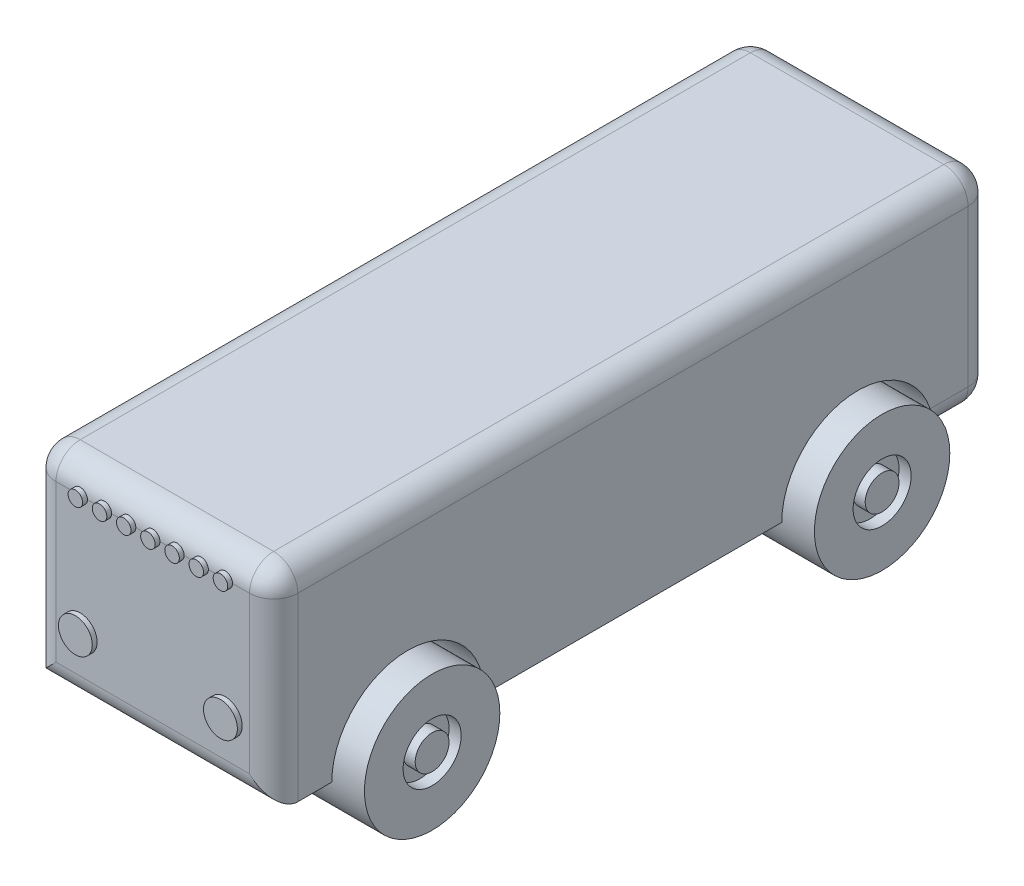
SolidWorks part; units mm, degrees
ref_plane "Спереди" through (0, 0, 0) normal (0, 0, 1) x (1, 0, 0)
ref_plane "Сверху" through (0, 0, 0) normal (0, 1, 0) x (1, 0, 0)
ref_plane "Справа" through (0, 0, 0) normal (1, 0, 0) x (0, 0, -1)
sketch "Эскиз1" plane through (0, 0, 0) normal (1, 0, 0) x (0, 0, -1)
  line L0 (-148.5757, -17.3338) -> (-124.5379, -17.3338)
  line L2 (-148.5757, 17.3338) -> (-148.5757, -17.3338)
  line L3 (-148.5757, -17.3338) -> (-124.5379, -17.3338)
  line L4 (148.5757, 17.3338) -> (148.5757, -17.3338)
  line L9 (124.5379, -17.3338) -> (148.5757, -17.3338)
  line L11 (-148.5757, 17.3338) -> (-148.5757, 32.3338)
  line L12 (-148.5757, 32.3338) -> (148.5757, 32.3338)
  line L13 (148.5757, 17.3338) -> (148.5757, 32.3338)
  line L15 (-61.5379, -17.3338) -> (61.5379, -17.3338)
  arc A0 (-61.5379, -17.3338) -> (-124.5379, -17.3338) centre (-93.0379, -17.3338) ccw
  arc A1 (61.5379, -17.3338) -> (124.5379, -17.3338) centre (93.0379, -17.3338) cw
  point P0 (0, 0)
  dimension "D3" = 15
extrude "Бобышка-Вытянуть1" add sketch "Эскиз1" along normal blind 100 contours L15 A1 L9 L4 L13 L12 L11 L2 L0 A0
sketch "Эскиз2" plane through (0, 0, 0) normal (1, 0, 0) x (0, 0, -1)
  line L0 (-124.5379, -17.3338) -> (-61.5379, -17.3338) construction
  line L1 (61.5379, -17.3338) -> (124.5379, -17.3338) construction
  circle A0 centre (-93.0379, -17.3338) radius 28
  circle A1 centre (93.0379, -17.3338) radius 28
extrude "Бобышка-Вытянуть2" add sketch "Эскиз2" along normal blind 30 and the other way blind 10 separate body
sketch "Эскиз3" plane through (100, 0, 0) normal (1, 0, 0) x (0, 0, -1)
  line L0 (-124.5379, -17.3338) -> (-61.5379, -17.3338) construction
  line L1 (61.5379, -17.3338) -> (124.5379, -17.3338) construction
  arc A0 (-61.5379, -17.3338) -> (-124.5379, -17.3338) centre (-93.0379, -17.3338) ccw construction
  circle A1 centre (-93.0379, -17.3338) radius 28
  circle A2 centre (93.0379, -17.3338) radius 28
extrude "Бобышка-Вытянуть3" add sketch "Эскиз3" against normal blind 30 and the other way blind 10 separate body
sketch "Эскиз4" plane through (0, -17.3338, 0) normal (0, -1, 0) x (1, 0, 0)
  line L0 (0, 61.5379) -> (50, 61.5379) construction
  line L1 (100, 61.5379) -> (0, 61.5379) construction
  line L3 (100, 124.5379) -> (0, 124.5379) construction
  line L4 (0, 0) -> (150.4034, 0) construction
  line L5 (45, 61.5379) -> (55, 61.5379)
  line L6 (45, 61.5379) -> (45, 88.0379)
  line L7 (45, 124.5379) -> (55, 124.5379)
  line L8 (55, 61.5379) -> (55, 88.0379)
  line L11 (70.0613, 88.0379) -> (55, 88.0379)
  line L12 (70.0613, 88.0379) -> (70.0613, 98.0379)
  line L13 (70.0613, 98.0379) -> (55, 98.0379)
  line L14 (29.9387, 88.0379) -> (29.9387, 98.0379)
  line L17 (150.4034, 0) -> (-75.8776, 0) construction
  line L18 (45, -61.5379) -> (55, -61.5379)
  line L19 (45, -124.5379) -> (55, -124.5379)
  line L20 (29.9387, -88.0379) -> (29.9387, -98.0379)
  line L21 (70.0613, -88.0379) -> (70.0613, -98.0379)
  line L22 (70.0613, -88.0379) -> (55, -88.0379)
  line L23 (70.0613, -98.0379) -> (55, -98.0379)
  line L24 (55, -61.5379) -> (55, -88.0379)
  line L25 (45, -61.5379) -> (45, -88.0379)
  line L26 (45, -98.0379) -> (45, -124.5379)
  line L27 (45, -98.0379) -> (29.9387, -98.0379)
  line L28 (45, -88.0379) -> (29.9387, -88.0379)
  line L29 (55, -98.0379) -> (55, -124.5379)
  line L30 (45, 88.0379) -> (29.9387, 88.0379)
  line L32 (45, 98.0379) -> (45, 124.5379)
  line L33 (45, 98.0379) -> (29.9387, 98.0379)
  line L34 (55, 98.0379) -> (55, 124.5379)
  point P5 (50, 93.0379)
  point P13 (50, 93.0379)
  dimension "D1" = 10
  dimension "D2" = 10
extrude "Бобышка-Вытянуть5" add sketch "Эскиз4" against normal blind 10 contours L5 L8 L11 L12 L13 L34 L7 L32 L33 L14 L30 L6 | L18 L24 L22 L21 L23 L29 L19 L26 L27 L20 L28 L25
sketch "Эскиз7" plane through (0, 0, 0) normal (1, 0, 0) x (0, 0, -1)
  line L1 (-148.5757, 32.3338) -> (148.5757, 32.3338)
  line L2 (-148.5757, 32.3338) -> (-148.5757, 57.3338)
  line L3 (-138.5757, 67.3338) -> (138.5757, 67.3338)
  line L4 (148.5757, 32.3338) -> (148.5757, 57.3338)
  arc A0 (-148.5757, 57.3338) -> (-138.5757, 67.3338) centre (-138.5757, 57.3338) cw
  arc A1 (148.5757, 57.3338) -> (138.5757, 67.3338) centre (138.5757, 57.3338) ccw
  point P7 (-148.5757, 67.3338)
  dimension "D2" = 10
  dimension "D3" = 10
  dimension "D1" = 35
extrude "Бобышка-Вытянуть7" add sketch "Эскиз7" along normal blind 100
sketch "Эскиз9" plane through (0, 0, 0) normal (0, 0, 1) x (1, 0, 0)
  line L0 (0, -7.3248) -> (50, -7.3248)
  line L1 (0, -17.3338) -> (0, 57.3338) construction
  line L2 (50, -7.3248) -> (100, -7.3248)
  line L3 (100, -17.3338) -> (100, 57.3338) construction
  line L4 (100, -7.3248) -> (75, -7.3248)
  line L5 (25, -7.3248) -> (50, -7.3248)
  line L6 (25, -7.3248) -> (12.5, -7.3248)
  line L7 (75, -7.3248) -> (87.5, -7.3248)
  dimension "D1" = 50
  dimension "D2" = 12.5
  dimension "D3" = 12.5
fillet "Скругление1" radius 10 11 edges at (100, 20, -148.5757) (0, 64.4049, -145.6468) (100, 64.4049, -145.6468) (0, 67.3338, 0) (100, 67.3338, 0) (0, 64.4049, 145.6468) (100, 64.4049, 145.6468) (0, 20, -148.5757) (100, 20, 148.5757) (50, -17.3338, 148.5757) (0, 20, 148.5757)
fillet "Скругление2" radius 10 5 edges at (100, -17.3338, -131.5568) (97.0711, -17.3338, -145.6468) (0, -17.3338, -131.5568) (2.9289, -17.3338, -145.6468) (50, -17.3338, -148.5757)
sketch "Эскиз10" plane through (0, 0, 148.5757) normal (0, 0, 1) x (1, 0, 0)
  line L0 (10, -1.617) -> (50, -1.617)
  line L1 (10, 57.3338) -> (10, -7.3338) construction
  line L2 (50, -1.617) -> (90, -1.617)
  line L3 (90, -7.3338) -> (90, 57.3338) construction
  line L4 (90, -1.617) -> (70, -1.617)
  line L5 (70, -1.617) -> (30, -1.617)
  line L6 (30, -1.617) -> (20, -1.617)
  line L7 (50, 48.2611) -> (50, -1.617)
  line L8 (90, 57.3338) -> (10, 57.3338) construction
  line L9 (15, 60.3338) -> (85, 60.3338)
  line L10 (15, 60.3338) -> (15, 54.3338)
  line L11 (15, 54.3338) -> (85, 54.3338)
  line L12 (85, 60.3338) -> (85, 54.3338)
  circle A0 centre (20, 8.3202) radius 7
  circle A1 centre (80, 8.3202) radius 7
  circle A2 centre (50, 57.3338) radius 3
  circle A3 centre (60, 57.3338) radius 3
  circle A4 centre (70, 57.3338) radius 3
  circle A5 centre (80, 57.3338) radius 3
  circle A6 centre (40, 57.3338) radius 3
  circle A7 centre (30, 57.3338) radius 3
  circle A8 centre (20, 57.3338) radius 3
  point P15 (50, 57.3338)
  line M14 (90, 57.3338) -> (10, 57.3338)
  dimension "D3" = 70
  dimension "D1" = 40
  dimension "D2" = 10
  dimension "D4" = 6
  dimension "D5" = 4
  dimension "D6" = 4
extrude "Бобышка-Вытянуть9" add sketch "Эскиз10" along normal blind 2 contours A0 | A1 | A8 M14 | A8 M14 | A7 M14 | A7 M14 | A6 M14 | A6 M14 | A2 M14 | A2 M14 | A3 M14 | A3 M14 | A4 M14 | A4 M14 | A5 M14 | A5 M14
sketch "Эскиз11" plane through (-10, 0, 0) normal (-1, 0, 0) x (0, 0, 1)
  circle A0 centre (-93.0379, -17.3338) radius 12
extrude "Вырез-Вытянуть1" cut sketch "Эскиз11" against normal blind 5
sketch "Эскиз12" plane through (-10, 0, 0) normal (-1, 0, 0) x (0, 0, 1)
  circle A0 centre (-93.0379, -17.3338) radius 7
extrude "Бобышка-Вытянуть11" add sketch "Эскиз12" against normal blind 5
sketch "Эскиз13" plane through (-10, 0, 0) normal (-1, 0, 0) x (0, 0, 1)
  circle A0 centre (93.0379, -17.3338) radius 12
extrude "Вырез-Вытянуть2" cut sketch "Эскиз13" against normal blind 5
sketch "Эскиз14" plane through (-5, 0, 0) normal (-1, 0, 0) x (0, 0, 1)
  circle A0 centre (93.0379, -17.3338) radius 7
extrude "Бобышка-Вытянуть12" add sketch "Эскиз14" along normal blind 5
sketch "Эскиз15" plane through (110, 0, 0) normal (1, 0, 0) x (0, 0, -1)
  circle A0 centre (-93.0379, -17.3338) radius 12
extrude "Вырез-Вытянуть3" cut sketch "Эскиз15" against normal blind 5
sketch "Эскиз16" plane through (105, 0, 0) normal (1, 0, 0) x (0, 0, -1)
  circle A0 centre (-93.0379, -17.3338) radius 7
extrude "Бобышка-Вытянуть13" add sketch "Эскиз16" along normal blind 5
sketch "Эскиз17" plane through (110, 0, 0) normal (1, 0, 0) x (0, 0, -1)
  circle A0 centre (93.0379, -17.3338) radius 12
extrude "Вырез-Вытянуть4" cut sketch "Эскиз17" against normal blind 5
sketch "Эскиз18" plane through (105, 0, 0) normal (1, 0, 0) x (0, 0, -1)
  circle A0 centre (93.0379, -17.3338) radius 7
extrude "Бобышка-Вытянуть14" add sketch "Эскиз18" along normal blind 5
sketch "Эскиз21" plane through (0, 0, -148.5757) normal (0, 0, -1) x (-1, 0, 0)
  line L0 (-50, 57.3338) -> (-50, -7.3248) construction
  line L1 (-90, 57.3338) -> (-10, 57.3338) construction
  line L2 (-90, 25) -> (-10, 25) construction
  line L3 (-90, 57.3338) -> (-90, -7.3338) construction
  line L4 (-10, -7.3338) -> (-10, 57.3338) construction
  line L6 (-78.6888, -7.3248) -> (-21.3112, -7.3248)
  line L7 (-78.6888, -7.3248) -> (-78.6888, 57.3338)
  line L8 (-78.6888, 57.3338) -> (-21.3112, 57.3338)
  line L9 (-21.3112, -7.3248) -> (-21.3112, 57.3338)
  line L10 (-78.6888, -7.3248) -> (-21.3112, 57.3338) construction
  line L11 (-78.6888, 57.3338) -> (-21.3112, -7.3248) construction
  point P11 (-50, 25.0045)
extrude "Бобышка-Вытянуть15" add sketch "Эскиз21" along normal blind 1
